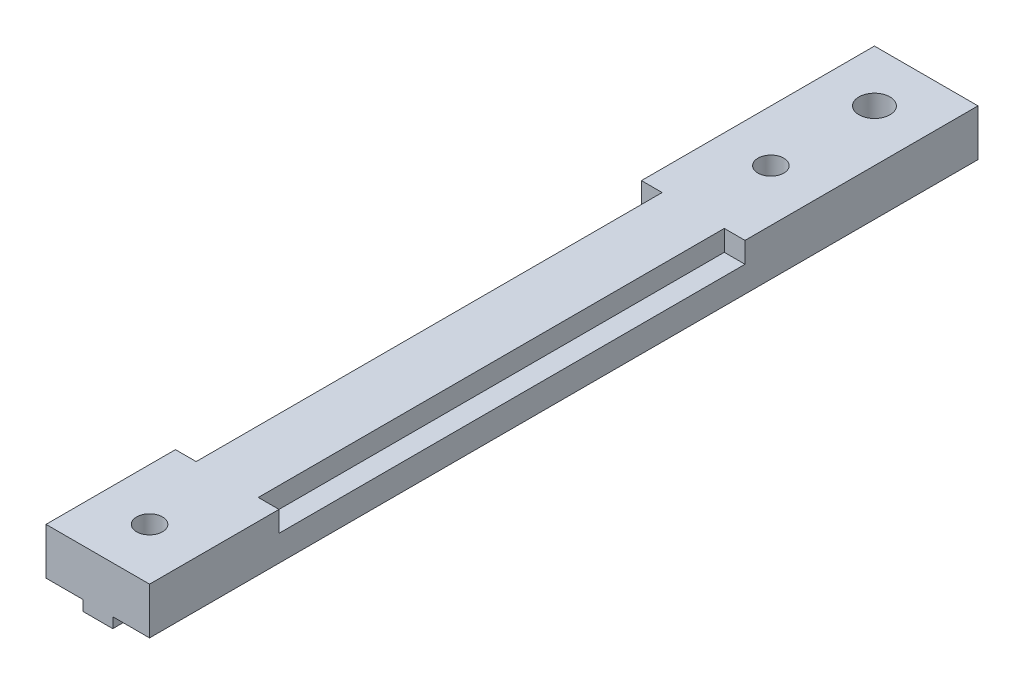
SolidWorks part; units mm, degrees
ref_plane "Front Plane" through (0, 0, 0) normal (0, 0, 1) x (1, 0, 0)
ref_plane "Top Plane" through (0, 0, 0) normal (0, 1, 0) x (1, 0, 0)
ref_plane "Right Plane" through (0, 0, 0) normal (1, 0, 0) x (0, 0, -1)
sketch "Sketch1" plane through (0, 0, 0) normal (0, 0, 1) x (1, 0, 0)
  line L0 (-5, 0) -> (5, 0)
  line L1 (5, 0) -> (5, -4.5)
  line L2 (5, -4.5) -> (1.45, -4.5)
  line L3 (1.45, -4.5) -> (1.45, -5.5)
  line L4 (1.45, -5.5) -> (-1.45, -5.5)
  line L5 (-1.45, -5.5) -> (-1.45, -4.5)
  line L6 (-1.45, -4.5) -> (-5, -4.5)
  line L7 (-5, -4.5) -> (-5, 0)
  point P9 (0, 0)
  dimension "D1" = 10
  dimension "D2" = 4.5
  dimension "D3" = 1
  dimension "D4" = 2.9
extrude "Main" add sketch "Sketch1" along normal blind 80
sketch "Sketch2" plane through (0, 0, 0) normal (0, 1, 0) x (1, 0, 0)
  line L0 (5, -80) -> (-5, -80) construction
  line L1 (5, 0) -> (-5, 0) construction
  circle A0 centre (0, -75) radius 1.25
  circle A1 centre (0, -15) radius 1.25
  circle A2 centre (0, -5) radius 1.5
  dimension "D1" = 2.5
  dimension "D4" = 3
  dimension "D2" = 5
  dimension "D3" = 60
  dimension "D5" = 5
extrude "MakerBeamFixHole" cut sketch "Sketch2" against normal through all
sketch "Sketch3" plane through (0, 0, 0) normal (0, 1, 0) x (1, 0, 0)
  line L0 (-5, -80) -> (-5, 0) construction
  line L1 (-5, -22.5) -> (-3, -22.5)
  line L2 (-5, -22.5) -> (-5, -67.5)
  line L3 (-5, -67.5) -> (-3, -67.5)
  line L4 (-3, -22.5) -> (-3, -67.5)
  line L5 (5, -80) -> (5, 0) construction
  line L6 (3, -22.5) -> (5, -22.5)
  line L7 (3, -22.5) -> (3, -67.5)
  line L8 (3, -67.5) -> (5, -67.5)
  line L9 (5, -22.5) -> (5, -67.5)
  line L10 (5, -80) -> (-5, -80) construction
  dimension "D1" = 6
  dimension "D2" = 45
  dimension "D3" = 12.5
extrude "PinHoles" cut sketch "Sketch3" against normal blind 2
